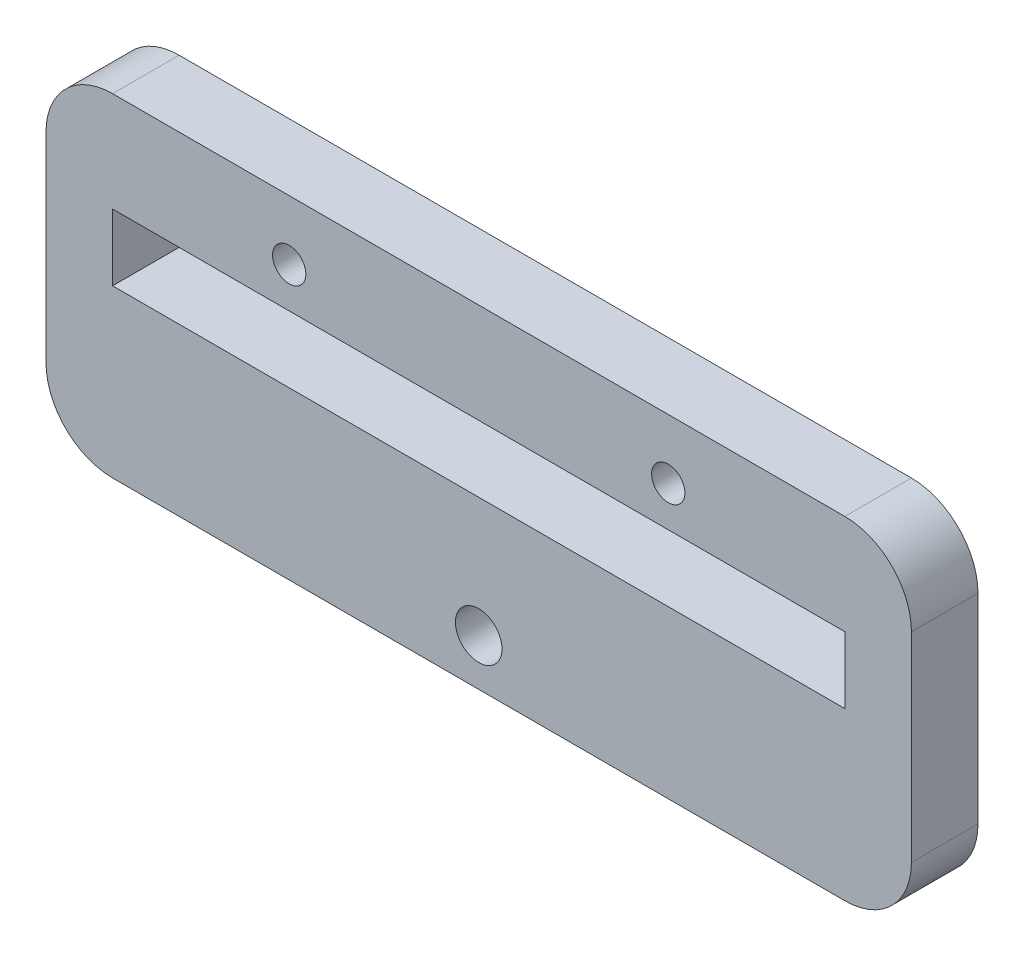
SolidWorks part; units mm, degrees
ref_plane "Front Plane" through (0, 0, 0) normal (0, 0, 1) x (1, 0, 0)
ref_plane "Top Plane" through (0, 0, 0) normal (0, 1, 0) x (1, 0, 0)
ref_plane "Right Plane" through (0, 0, 0) normal (1, 0, 0) x (0, 0, -1)
sketch "Sketch1" plane through (0, 0, 0) normal (0, 0, 1) x (1, 0, 0)
  line L1 (0, 0) -> (130, 0)
  line L2 (0, 0) -> (0, 50)
  line L3 (0, 50) -> (130, 50)
  line L4 (130, 0) -> (130, 50)
  line L5 (10, 25) -> (120, 25)
  line L6 (10, 25) -> (10, 35)
  line L7 (10, 35) -> (120, 35)
  line L8 (120, 25) -> (120, 35)
  circle A0 centre (36.53, 41.03) radius 2.5
  circle A1 centre (93.47, 41.03) radius 2.5
  circle A2 centre (65, 7) radius 3.5
  dimension "D11" = 5
  dimension "D12" = 5
  dimension "D15" = 7
  dimension "D1" = 50
  dimension "D2" = 130
  dimension "D3" = 110
  dimension "D4" = 6.03
  dimension "D5" = 6.03
  dimension "D6" = 10
  dimension "D7" = 25
  dimension "D8" = 10
  dimension "D9" = 56.94
  dimension "D10" = 36.53
  dimension "D13" = 65
  dimension "D14" = 7
extrude "Boss-Extrude2" add sketch "Sketch1" along normal blind 10
fillet "Fillet1" radius 10 4 edges at (0, 0, 5) (130, 0, 5) (0, 50, 5) (130, 50, 5)
